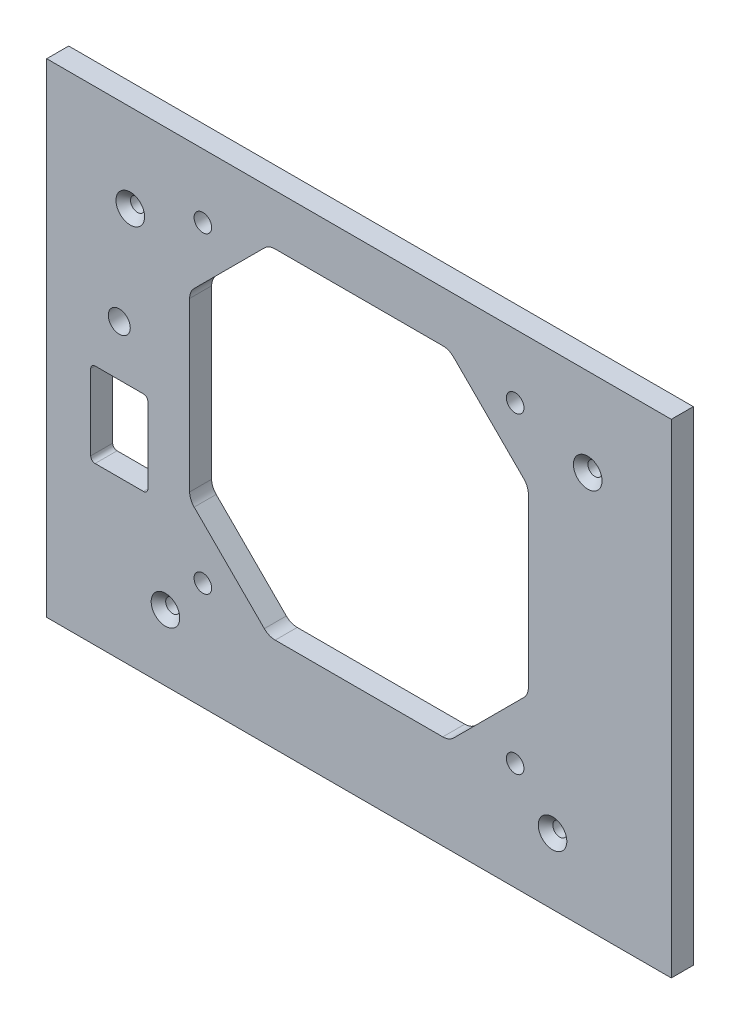
SolidWorks part; units mm, degrees
material "Polycarbonate (PC)"
ref_plane "Front Plane" through (0, 0, 0) normal (0, 0, 1) x (1, 0, 0)
ref_plane "Top Plane" through (0, 0, 0) normal (0, 1, 0) x (1, 0, 0)
ref_plane "Right Plane" through (0, 0, 0) normal (1, 0, 0) x (0, 0, -1)
sketch "Sketch1" plane through (0, 0, 0) normal (0, 0, 1) x (1, 0, 0)
  line L1 (71, -55) -> (-71, -55)
  line L2 (71, -55) -> (71, 55)
  line L3 (71, 55) -> (-71, 55)
  line L4 (-71, -55) -> (-71, 55)
  line L5 (71, -55) -> (-71, 55) construction
  line L6 (71, 55) -> (-71, -55) construction
  point P0 (0, 0)
  dimension "D1" = 142
  dimension "D2" = 110
extrude "Sheet" add sketch "Sketch1" along normal mid plane 5
sketch "Sketch7" plane through (0, 0, 2.5) normal (0, 0, 1) x (1, 0, 0)
  line L0 (-20.5, 43.5) -> (-38.5, 25.5)
  line L1 (20.5, -33.5) -> (-20.5, -33.5)
  line L2 (38.5, -15.5) -> (38.5, 25.5)
  line L3 (20.5, 43.5) -> (-20.5, 43.5)
  line L4 (-38.5, -15.5) -> (-38.5, 25.5)
  line L5 (38.5, -33.5) -> (-38.5, 43.5) construction
  line L6 (38.5, 43.5) -> (-38.5, -33.5) construction
  line L7 (-20.5, -33.5) -> (-38.5, -15.5)
  line L8 (38.5, -15.5) -> (20.5, -33.5)
  line L9 (38.5, 25.5) -> (20.5, 43.5)
  circle A0 centre (0, 5) radius 38.5 construction
  circle A1 centre (-35.5, -30.5) radius 2
  circle A2 centre (35.5, -30.5) radius 2
  circle A3 centre (35.5, 40.5) radius 2
  circle A4 centre (-35.5, 40.5) radius 2
  dimension "D3" = 4
  dimension "D10" = 77
  dimension "D2" = 5
  dimension "D4" = 71
  dimension "D5" = 71
  dimension "D11" = 77
extrude "FanHoles" cut sketch "Sketch7" against normal through all
chamfer "FanChamfer" [suppressed] distance 3 angle 45
fillet "Fillet1" radius 3.5 8 edges at (38.5, 25.5, 0) (38.5, -15.5, 0) (20.5, -33.5, 0) (-38.5, -15.5, 0) (-38.5, 25.5, 0) (-20.5, 43.5, 0) (20.5, 43.5, 0) (-20.5, -33.5, 0)
hole_wizard "Ø3.2 (3.2) TopMountHoles" positions "Sketch9" profile "Sketch10" hole size "Ø3.2" standard "ANSI Metric" end condition through all
sketch "Sketch9" plane through (0, 0, 2.5) normal (0, 0, 1) x (1, 0, 0)
  line L0 (71, 55) -> (-71, 55) construction
  line L1 (-71, 55) -> (-71, -55) construction
  line L2 (71, -55) -> (71, 55) construction
  point P0 (-52, 35)
  point P2 (52, 35)
  dimension "D1" = 20
  dimension "D2" = 19
  dimension "D3" = 19
sketch "Sketch10" plane through (-52, 35, 2.5) normal (1, 0, 0) x (0, -1, 0)
  line L0 (0, 0) -> (0, 5)
  line L1 (0, 5) -> (1.6, 5)
  line L2 (1.6, 5) -> (1.6, 1.65)
  line L3 (1.6, 1.65) -> (3.25, 0)
  line L5 (3.25, 0) -> (0, 0)
  line L6 (-1.6, 1.65) -> (-3.25, 0) construction
  line L11 (0, -6.35) -> (0, 107.95) construction
  dimension "Thru Hole Dia." = 3.2
  dimension "Thru Hole Depth" = 5
  dimension "Near C'Sink Dia." = 6.5
  dimension "Near C'Sink Angle" = 90
hole_wizard "Ø3.2 (3.2) BottomMountHoles" positions "Sketch11" profile "Sketch12" hole size "Ø3.2" standard "ANSI Metric" end condition through all
sketch "Sketch11" plane through (0, 0, 2.5) normal (0, 0, 1) x (1, 0, 0)
  line L0 (-71, -55) -> (71, -55) construction
  line L1 (-71, 55) -> (-71, -55) construction
  line L2 (71, -55) -> (71, 55) construction
  point P0 (-44, -40)
  point P2 (44, -40)
  dimension "D1" = 15
  dimension "D2" = 27
  dimension "D3" = 27
sketch "Sketch12" plane through (-44, -40, 2.5) normal (1, 0, 0) x (0, -1, 0)
  line L0 (0, 0) -> (0, 5)
  line L1 (0, 5) -> (1.6, 5)
  line L2 (1.6, 5) -> (1.6, 1.65)
  line L3 (1.6, 1.65) -> (3.25, 0)
  line L5 (3.25, 0) -> (0, 0)
  line L6 (-1.6, 1.65) -> (-3.25, 0) construction
  line L11 (0, -6.35) -> (0, 107.95) construction
  dimension "Thru Hole Dia." = 3.2
  dimension "Thru Hole Depth" = 5
  dimension "Near C'Sink Dia." = 6.5
  dimension "Near C'Sink Angle" = 90
sketch "Sketch13" plane through (0, 0, 2.5) normal (0, 0, 1) x (1, 0, 0)
  line L0 (-71, 55) -> (-71, -55) construction
  line L1 (-60, 0) -> (-49, 0)
  line L2 (-61, -1) -> (-61, -18.2)
  line L3 (-60, -19.2) -> (-49, -19.2)
  line L4 (-48, -1) -> (-48, -18.2)
  line L5 (71, 55) -> (-71, 55) construction
  arc A0 (-49, -19.2) -> (-48, -18.2) centre (-49, -18.2) ccw
  arc A1 (-61, -18.2) -> (-60, -19.2) centre (-60, -18.2) ccw
  arc A2 (-49, 0) -> (-48, -1) centre (-49, -1) cw
  arc A3 (-60, 0) -> (-61, -1) centre (-60, -1) ccw
  point P8 (-61, -19.2)
  point P11 (-48, 0)
  point P14 (-61, 0)
  dimension "D3" = 1
  dimension "D1" = 13
  dimension "D2" = 19.2
  dimension "D4" = 10
  dimension "D5" = 55
extrude "SwitchSlot" cut sketch "Sketch13" against normal through all
sketch "Sketch8" plane through (0, 0, 2.5) normal (0, 0, 1) x (1, 0, 0)
  line L0 (-49, 0) -> (-60, 0) construction
  circle A0 centre (-54.5, 11.5) radius 2.5
  point P7 (-54.5, 0)
  dimension "D1" = 11.5
  dimension "D2" = 5
extrude "LEDHole" cut sketch "Sketch8" against normal through all
equation "\"D3@Sketch9\"=\"D2@Sketch9\""
equation "\"D3@Sketch11\"=\"D2@Sketch11\""
